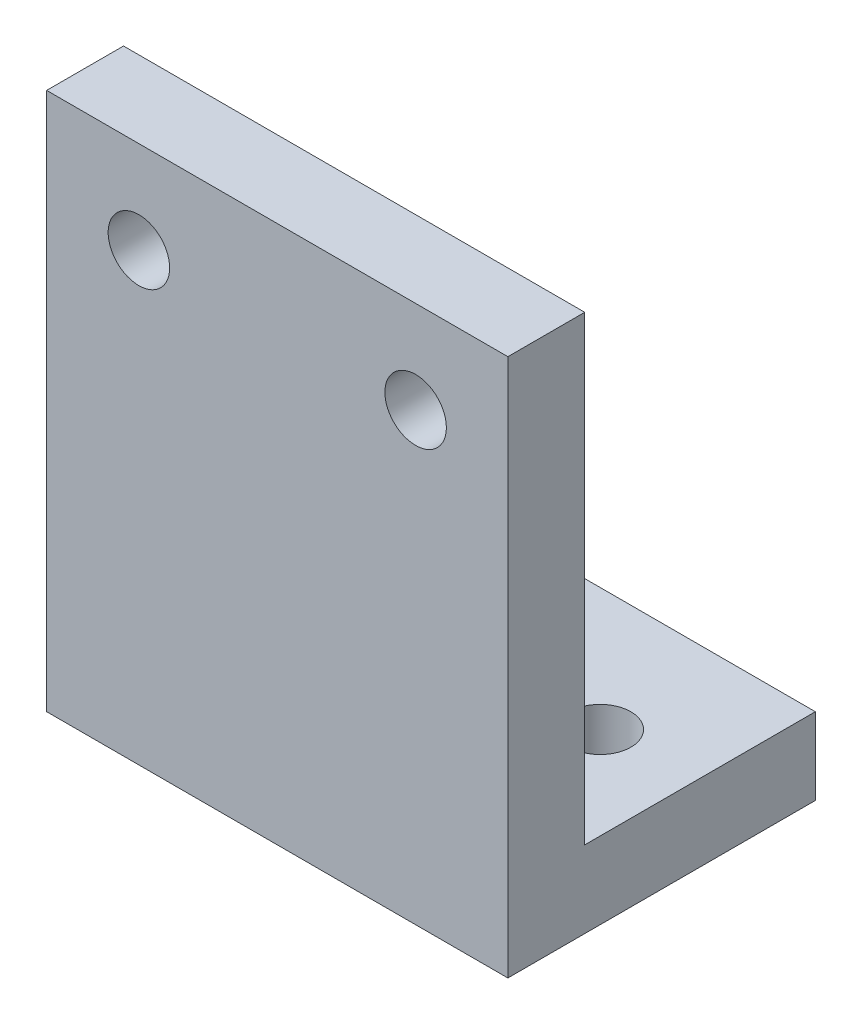
SolidWorks part; units mm, degrees
ref_plane "Plano frontal" through (0, 0, 0) normal (0, 0, 1) x (1, 0, 0)
ref_plane "Plano superior" through (0, 0, 0) normal (0, 1, 0) x (1, 0, 0)
ref_plane "Plano direito" through (0, 0, 0) normal (1, 0, 0) x (0, 0, -1)
sketch "Esboço1" plane through (0, 0, 0) normal (0, 0, 1) x (1, 0, 0)
  line L0 (0, -25.0231) -> (0, 9.0938) construction
  line L1 (-15, -15) -> (15, -15)
  line L2 (-15, -15) -> (-15, 15)
  line L3 (-15, 15) -> (15, 15)
  line L4 (15, -15) -> (15, 15)
  line L5 (-15, -15) -> (15, 15) construction
  line L6 (-15, 15) -> (15, -15) construction
  line L7 (9, 9) -> (-9, 9) construction
  circle A0 centre (-9, 9) radius 2
  circle A1 centre (9, 9) radius 2
  point P0 (0, 0)
  point P8 (0, -27.5)
  point P18 (0, 9)
  point P19 (0, 15)
  dimension "D6" = 4
  dimension "D3" = 30
  dimension "D4" = 30
  dimension "D5" = 6
  dimension "D7" = 18
extrude "Ressalto-extrusão1" add sketch "Esboço1" along normal blind 5
sketch "Esboço2" plane through (0, -15, 0) normal (0, -1, 0) x (1, 0, 0)
  line L0 (0, -15) -> (0, 5) construction
  line L1 (-15, -15) -> (15, -15)
  line L2 (-15, -15) -> (-15, 5)
  line L3 (-15, 5) -> (15, 5)
  line L4 (15, -15) -> (15, 5)
  line L5 (-15, -15) -> (15, 5) construction
  line L6 (-15, 5) -> (15, -15) construction
  circle A0 centre (-9, -7) radius 2
  circle A1 centre (9, -7) radius 2
  point P0 (0, -5)
  dimension "D4" = 4
  dimension "D1" = 20
  dimension "D2" = 18
  dimension "D3" = 8
extrude "Ressalto-extrusão2" add sketch "Esboço2" along normal blind 5
